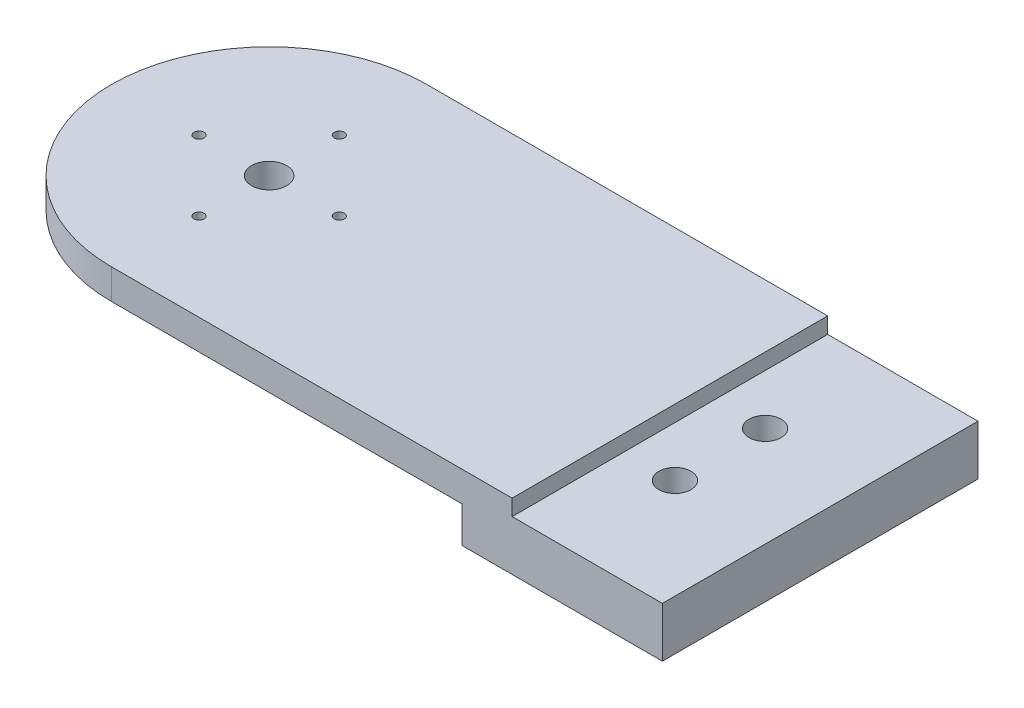
SolidWorks part; units mm, degrees
ref_plane "前视基准面" through (0, 0, 0) normal (0, 0, 1) x (1, 0, 0)
ref_plane "上视基准面" through (0, 0, 0) normal (0, 1, 0) x (1, 0, 0)
ref_plane "右视基准面" through (0, 0, 0) normal (1, 0, 0) x (0, 0, -1)
sketch "草图1" plane through (0, 0, 0) normal (0, 1, 0) x (1, 0, 0)
  line L0 (0, -15.75) -> (55, -15.75)
  line L1 (55, -15.75) -> (55, 15.75)
  line L2 (55, 15.75) -> (0, 15.75)
  arc A0 (0, 15.75) -> (0, -15.75) centre (0, 0) ccw
  dimension "D1" = 31.5
  dimension "D2" = 55
extrude "凸台-拉伸1" add sketch "草图1" along normal blind 3
sketch "草图3" plane through (0, 0, 0) normal (0, -1, 0) x (1, 0, 0)
  line L0 (0, 15.75) -> (55, 15.75) construction
  line L1 (35, 15.75) -> (55, 15.75)
  line L2 (35, 15.75) -> (35, -15.75)
  line L3 (35, -15.75) -> (55, -15.75)
  line L4 (55, 15.75) -> (55, -15.75)
  dimension "D1" = 20
extrude "凸台-拉伸2" add sketch "草图3" along normal blind 2
sketch "草图4" plane through (0, 0, 0) normal (0, -1, 0) x (1, 0, 0)
  circle A4 centre (0, 0) radius 7 construction
  circle A5 centre (0, 7) radius 0.5
  circle A6 centre (7, 0) radius 0.5
  circle A7 centre (0, -7) radius 0.5
  circle A8 centre (-7, 0) radius 0.5
  dimension "D1" = 1
  dimension "D2" = 1
  dimension "D3" = 1
  dimension "D4" = 1
  dimension "D5" = 14
extrude "切除-拉伸1" cut sketch "草图4" against normal blind 10
sketch "草图5" plane through (0, -2, 0) normal (0, -1, 0) x (1, 0, 0)
  line L0 (55, 0) -> (22.9219, 0) construction
  line L1 (55, -15.75) -> (55, 15.75) construction
  circle A0 centre (45, -4.5) radius 1.6
  circle A1 centre (45, 4.5) radius 1.6
  dimension "D1" = 9
  dimension "D2" = 10
  dimension "D3" = 3.2
extrude "切除-拉伸2" cut sketch "草图5" against normal blind 10
sketch "草图6" plane through (0, 0, 0) normal (0, -1, 0) x (1, 0, 0)
  circle A0 centre (0, 0) radius 1.75
  dimension "D1" = 3.5
extrude "切除-拉伸3" cut sketch "草图6" against normal blind 17
sketch "草图7" plane through (0, 0, 0) normal (0, -1, 0) x (1, 0, 0)
  line L3 (35, -15.75) -> (35, 15.75)
  line L4 (35, 15.75) -> (0, 15.75)
  line L5 (0, -15.75) -> (35, -15.75)
  line L6 (35, -15.75) -> (35, 15.75)
  line L7 (35, 15.75) -> (0, 15.75)
  line L8 (0, -15.75) -> (35, -15.75)
  arc A1 (0, 15.75) -> (0, -15.75) centre (0, 0) ccw
  arc A2 (0, 15.75) -> (0, -15.75) centre (0, 0) ccw
  dimension "D1" = 0
extrude "切除-拉伸4" cut sketch "草图7" against normal blind 1.6
sketch "草图8" plane through (0, 1.6, 0) normal (0, -1, 0) x (1, 0, 0)
  line L3 (0, -15.75) -> (35, -15.75)
  line L4 (35, -15.75) -> (35, 15.75)
  line L5 (35, 15.75) -> (0, 15.75)
  line L6 (0, -15.75) -> (35, -15.75)
  line L7 (35, -15.75) -> (35, 15.75)
  line L8 (35, 15.75) -> (0, 15.75)
  arc A1 (0, 15.75) -> (0, -15.75) centre (0, 0) ccw
  arc A2 (0, 15.75) -> (0, -15.75) centre (0, 0) ccw
  dimension "D1" = 0
extrude "凸台-拉伸3" add sketch "草图8" against normal blind 3
sketch "草图9" plane through (35, 0, 0) normal (1, 0, 0) x (0, 0, -1)
  line L1 (-15.75, 4.6) -> (15.75, 4.6)
  line L2 (-15.75, 4.6) -> (-15.75, 3)
  line L3 (-15.75, 3) -> (15.75, 3)
  line L4 (15.75, 4.6) -> (15.75, 3)
extrude "凸台-拉伸4" add sketch "草图9" along normal blind 3
sketch "草图10" plane through (0, 1.6, 0) normal (0, -1, 0) x (1, 0, 0)
  circle A0 centre (0, 0) radius 1.75
  circle A1 centre (0, 7) radius 0.5
  circle A2 centre (7, 0) radius 0.5
  circle A3 centre (0, -7) radius 0.5
  circle A4 centre (-7, 0) radius 0.5
  dimension "D1" = 3.5
  dimension "D4" = 1
  dimension "D5" = 1
  dimension "D6" = 1
  dimension "D7" = 1
  dimension "D2" = 7
  dimension "D3" = 7
  dimension "D8" = 7
  dimension "D9" = 7
extrude "切除-拉伸5" cut sketch "草图10" against normal blind 10
sketch "草图12" plane through (0, 1.6, 0) normal (0, -1, 0) x (1, 0, 0)
  circle A0 centre (0, 0) radius 10
  dimension "D1" = 20
extrude "凸台-拉伸6" add sketch "草图12" along normal blind 1.6
sketch "草图13" plane through (38, 0, 0) normal (1, 0, 0) x (0, 0, -1)
  line L1 (-15.75, 4.6) -> (15.75, 4.6)
  line L2 (-15.75, 4.6) -> (-15.75, 3)
  line L3 (-15.75, 3) -> (15.75, 3)
  line L4 (15.75, 4.6) -> (15.75, 3)
extrude "凸台-拉伸7" add sketch "草图13" along normal blind 2
sketch "草图15" plane through (0, 0, 0) normal (0, -1, 0) x (1, 0, 0)
  circle A0 centre (0, 0) radius 1.75
  circle A1 centre (7, 0) radius 0.5
  circle A2 centre (0, -7) radius 0.5
  circle A3 centre (0, 7) radius 0.5
  circle A4 centre (-7, 0) radius 0.5
  dimension "D1" = 3.5
  dimension "D2" = 1
  dimension "D3" = 1
  dimension "D4" = 1
  dimension "D5" = 1
  dimension "D6" = 7
  dimension "D7" = 7
  dimension "D8" = 7
  dimension "D9" = 7
extrude "切除-拉伸6" cut sketch "草图15" against normal blind 12
